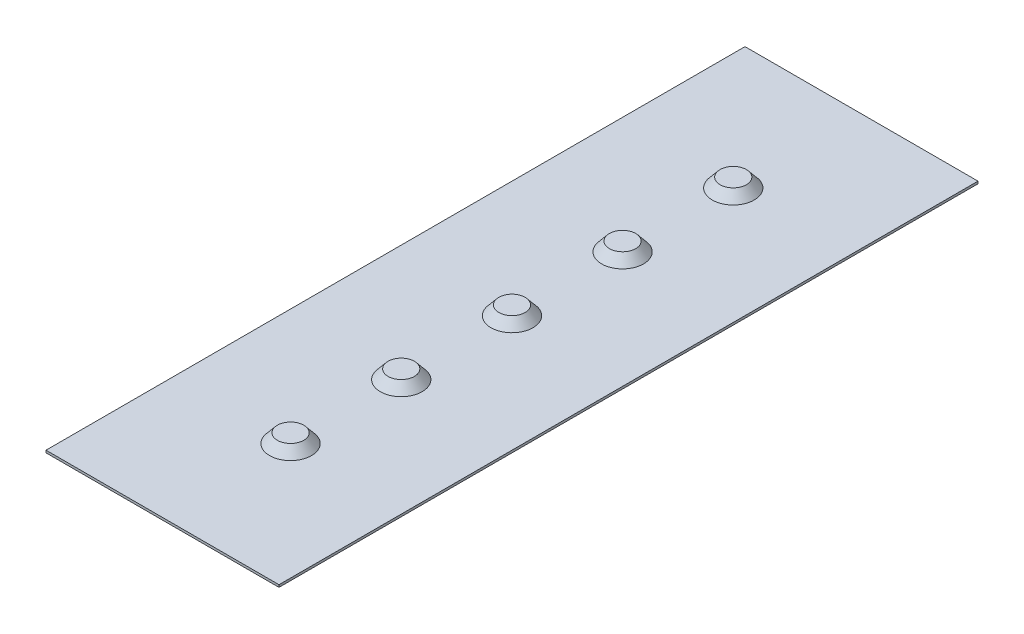
SolidWorks part; units mm, degrees
ref_plane "Front Plane" through (0, 0, 0) normal (0, 0, 1) x (1, 0, 0)
ref_plane "Top Plane" through (0, 0, 0) normal (0, 1, 0) x (1, 0, 0)
ref_plane "Right Plane" through (0, 0, 0) normal (1, 0, 0) x (0, 0, -1)
sketch "Sketch1" plane through (0, 0, 0) normal (0, 1, 0) x (1, 0, 0)
  line L0 (2.3566, -7.0697) -> (191.0557, -573.1672) construction
  line L1 (-8.9443, 26.8328) -> (191.0557, 26.8328)
  line L2 (-8.9443, 26.8328) -> (-8.9443, -573.1672)
  line L3 (-8.9443, -573.1672) -> (191.0557, -573.1672)
  line L4 (191.0557, 26.8328) -> (191.0557, -573.1672)
  line L5 (-8.9443, 26.8328) -> (-2.3566, 7.0697) construction
  point P0 (0, 0)
  dimension "600" = 600
  dimension "D2" = 200
extrude "Boss-Extrude1" add sketch "Sketch1" along normal blind 2
sketch "Sketch3" plane through (0, 2, 0) normal (0, 1, 0) x (1, 0, 0)
  line L0 (-8.9443, -273.1672) -> (191.0557, -273.1672) construction
  line L1 (-8.9443, 26.8328) -> (-8.9443, -573.1672) construction
  line L2 (191.0557, -573.1672) -> (191.0557, 26.8328) construction
  line L3 (91.0557, 26.8328) -> (91.0557, -573.1672) construction
  line L4 (191.0557, 26.8328) -> (-8.9443, 26.8328) construction
  line L5 (-8.9443, -573.1672) -> (191.0557, -573.1672) construction
  circle A0 centre (91.0557, -83.2465) radius 18
  circle A1 centre (91.0557, -178.2465) radius 18
  circle A2 centre (91.0557, -273.1672) radius 18
  circle A3 centre (91.0557, -368.2465) radius 18
  circle A4 centre (91.0557, -463.2465) radius 18
  point P12 (0, 0)
  point P23 (91.0557, -273.1672)
  point P24 (0, 0)
  point P25 (0, 0)
  point P26 (0, 0)
  point P27 (0, 0)
  point P28 (0, 0)
  point P29 (0, 0)
extrude "Boss-Extrude2" add sketch "Sketch3" along normal blind 8 draft 40
sketch "Orientation Sketch" plane through (0, 2, 0) normal (0, 1, 0) x (1, 0, 0)
  line L0 (191.0557, -573.1672) -> (191.0557, 26.8328) construction
  line L1 (191.0557, 26.8328) -> (-8.9443, 26.8328) construction
  line L2 (-8.9443, 26.8328) -> (-8.9443, -573.1672) construction
  line L3 (-8.9443, -573.1672) -> (191.0557, -573.1672) construction
  line L4 (191.0557, -573.1672) -> (191.0557, 26.8328) construction
  line L5 (191.0557, 26.8328) -> (-8.9443, 26.8328) construction
  line L6 (-8.9443, 26.8328) -> (-8.9443, -573.1672) construction
  line L7 (-8.9443, -573.1672) -> (191.0557, -573.1672) construction
  circle A0 centre (91.0557, -463.2465) radius 18 construction
  circle A1 centre (91.0557, -368.2465) radius 18 construction
  circle A2 centre (91.0557, -273.1672) radius 18 construction
  circle A3 centre (91.0557, -178.2465) radius 18 construction
  circle A4 centre (91.0557, -83.2465) radius 18 construction
  circle A5 centre (91.0557, -463.2465) radius 18
  circle A6 centre (91.0557, -368.2465) radius 18
  circle A7 centre (91.0557, -273.1672) radius 18
  circle A8 centre (91.0557, -178.2465) radius 18
  circle A9 centre (91.0557, -83.2465) radius 18
  point P19 (91.0557, -273.1672)
other "FormTool1"
